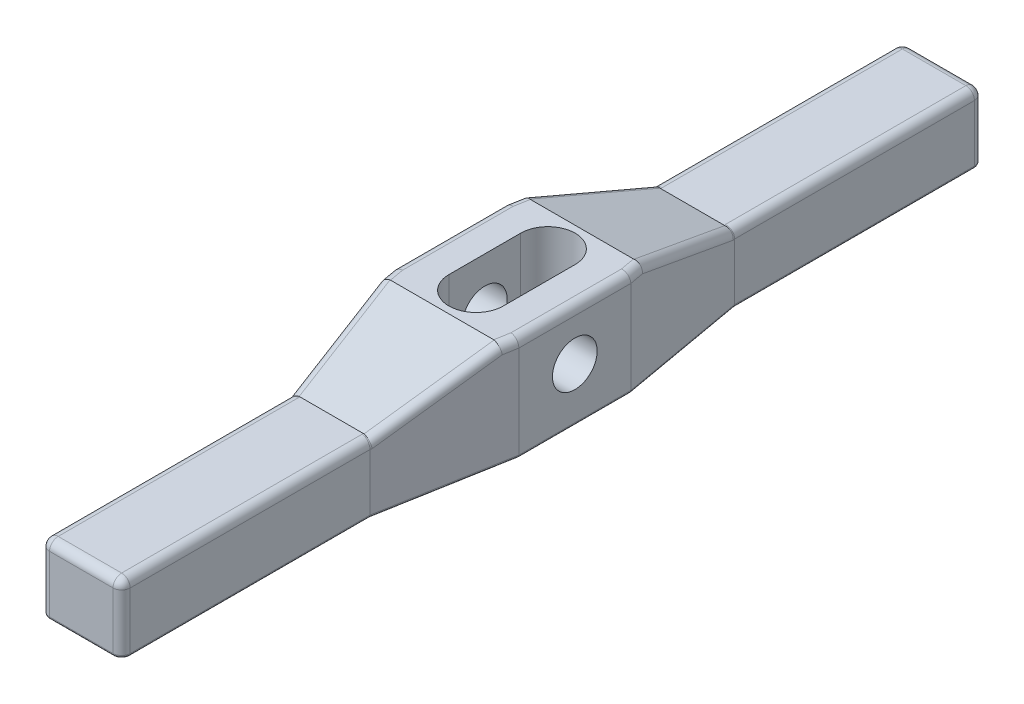
SolidWorks part; units mm, degrees
material "Alloy Steel"
ref_plane "Front Plane" through (0, 0, 0) normal (0, 0, 1) x (1, 0, 0)
ref_plane "Top Plane" through (0, 0, 0) normal (0, 1, 0) x (1, 0, 0)
ref_plane "Right Plane" through (0, 0, 0) normal (1, 0, 0) x (0, 0, -1)
sketch "Sketch1" plane through (0, 0, 0) normal (0, 1, 0) x (1, 0, 0)
  line L0 (0, 0) -> (68.8474, 0) construction
  line L1 (0, 0) -> (0, 75.643) construction
  line L2 (-7.1374, 76.2) -> (7.1374, 76.2)
  line L3 (7.1374, 76.2) -> (7.1374, 32.258)
  line L4 (7.1374, 32.258) -> (11.1125, 9.903)
  line L5 (11.1125, 9.903) -> (11.1125, -9.903)
  line L6 (7.1374, -32.258) -> (11.1125, -9.903)
  line L7 (7.1374, -76.2) -> (7.1374, -32.258)
  line L8 (-7.1374, -76.2) -> (7.1374, -76.2)
  line L9 (-7.1374, -76.2) -> (-7.1374, -32.258)
  line L10 (-7.1374, -32.258) -> (-11.1125, -9.903)
  line L11 (-11.1125, 9.903) -> (-11.1125, -9.903)
  line L12 (-7.1374, 32.258) -> (-11.1125, 9.903)
  line L13 (-7.1374, 76.2) -> (-7.1374, 32.258)
  line L14 (-4.8133, 6.35) -> (-4.8133, -6.35)
  line L15 (4.8133, 6.35) -> (4.8133, -6.35)
  arc A0 (4.8133, 6.35) -> (-4.8133, 6.35) centre (0, 6.35) ccw
  arc A1 (-4.8133, -6.35) -> (4.8133, -6.35) centre (0, -6.35) ccw
  dimension "D1" = 14.2748
  dimension "D2" = 152.4
  dimension "D3" = 22.225
  dimension "D4" = 43.942
  dimension "D5" = 19.8059
  dimension "D6" = 12.7
  dimension "D7" = 9.6266
extrude "Extrude1" add sketch "Sketch1" along normal blind 18.415
sketch "Sketch2" plane through (11.1125, 0, 0) normal (1, 0, 0) x (0, 0, -1)
  line L0 (0, 0) -> (0, 25.2428) construction
  line L1 (-9.903, 0) -> (9.903, 0) construction
  line L2 (76.2, 18.415) -> (12.3698, 18.415)
  line L3 (9.903, 18.415) -> (32.258, 18.415) construction
  line L4 (12.3698, 18.415) -> (31.9131, 12.065)
  line L5 (31.9131, 12.065) -> (76.2, 12.065)
  line L6 (76.2, 18.415) -> (76.2, 0) construction
  line L7 (76.2, 12.065) -> (76.2, 18.415)
  line L8 (32.258, 0) -> (76.2, 0) construction
  line L9 (-76.2, 12.065) -> (-76.2, 18.415)
  line L10 (-31.9131, 12.065) -> (-76.2, 12.065)
  line L11 (-12.3698, 18.415) -> (-31.9131, 12.065)
  line L12 (-76.2, 18.415) -> (-12.3698, 18.415)
  dimension "D1" = 12.3698
  dimension "D2" = 18
  dimension "D3" = 12.065
extrude "Cut-Extrude1" cut sketch "Sketch2" against normal through all
sketch "Sketch3" plane through (11.1125, 0, 0) normal (1, 0, 0) x (0, 0, -1)
  line L0 (-9.903, 0) -> (9.903, 0) construction
  circle A0 centre (0, 9.525) radius 3.956
  dimension "D1" = 7.9121
  dimension "D2" = 9.525
extrude "Cut-Extrude2" cut sketch "Sketch3" against normal through all
fillet "Fillet1" radius 1.524 4 edges at (-7.1374, 6.0325, -76.2) (7.1374, 6.0325, -76.2) (7.1374, 6.0325, 76.2) (-7.1374, 6.0325, 76.2)
fillet "Fillet2" radius 0.508 16 edges at (-7.1374, 0, 53.467) (-6.691, 0, 75.7536) (0, 0, 76.2) (6.691, 0, 75.7536) (-7.1374, 0, -53.467) (-6.691, 0, -75.7536) (0, 0, -76.2) (6.691, 0, -75.7536) (-9.125, 0, -21.0805) (-11.1125, 0, 0) (-9.125, 0, 21.0805) (7.1374, 0, 53.467) (9.125, 0, 21.0805) (11.1125, 0, 0) (9.125, 0, -21.0805) (7.1374, 0, -53.467)
fillet "Fillet3" radius 1.524 24 edges at (-6.691, 12.065, 75.7536) (0, 12.065, 76.2) (6.691, 12.065, 75.7536) (-7.1374, 12.065, -53.467) (-6.691, 12.065, -75.7536) (0, 12.065, -76.2) (6.691, 12.065, -75.7536) (-7.1681, 12.065, -32.0855) (-8.9363, 15.24, -22.1414) (-10.8932, 18.415, -11.1364) (-10.8932, 18.415, 11.1364) (-11.1125, 18.415, 0) (-8.9363, 15.24, 22.1414) (-7.1374, 12.065, 53.467) (-7.1681, 12.065, 32.0855) (7.1374, 12.065, 53.467) (7.1681, 12.065, 32.0855) (8.9363, 15.24, 22.1414) (10.8932, 18.415, 11.1364) (11.1125, 18.415, 0) (10.8932, 18.415, -11.1364) (7.1681, 12.065, -32.0855) (8.9363, 15.24, -22.1414) (7.1374, 12.065, -53.467)
